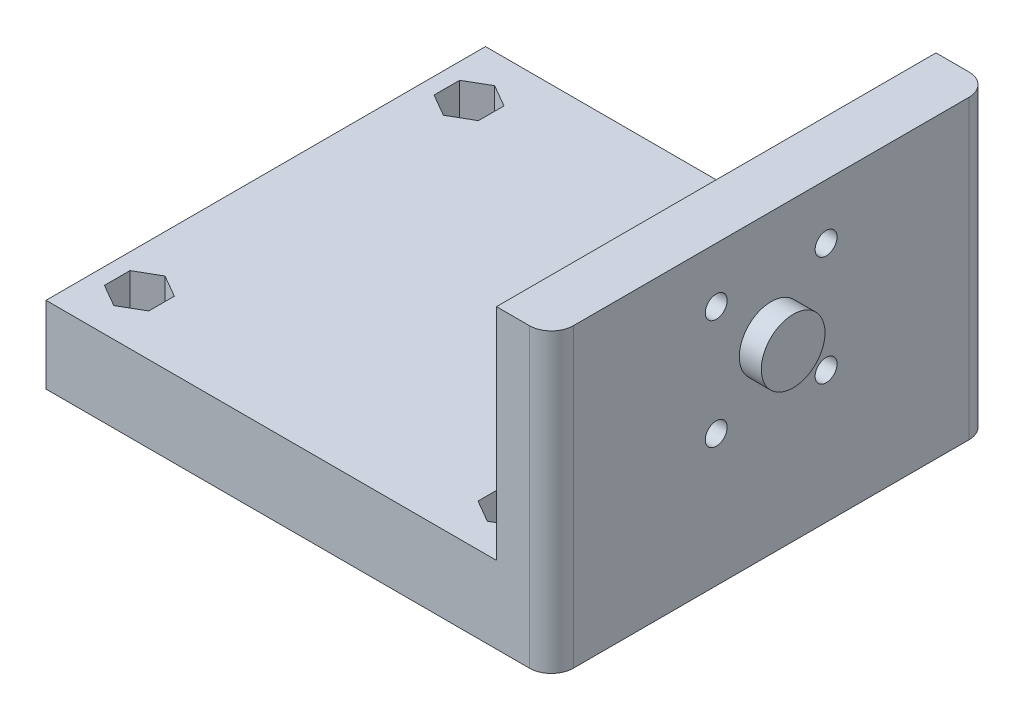
SolidWorks part; units mm, degrees
ref_plane "Plan de face" through (0, 0, 0) normal (0, 0, 1) x (1, 0, 0)
ref_plane "Plan de dessus" through (0, 0, 0) normal (0, 1, 0) x (1, 0, 0)
ref_plane "Plan de droite" through (0, 0, 0) normal (1, 0, 0) x (0, 0, -1)
sketch "Esquisse1" plane through (0, 0, 0) normal (0, 1, 0) x (1, 0, 0)
  line L1 (0, 20) -> (-5, 20)
  line L2 (0, 20) -> (0, -20)
  line L3 (0, -20) -> (-5, -20)
  line L4 (-5, 20) -> (-5, -20)
  dimension "D1" = 5
  dimension "D2" = 40
  dimension "D3" = 20
extrude "Boss.-Extru.1" add sketch "Esquisse1" against normal blind 27
sketch "Esquisse2" plane through (-5, 0, 0) normal (-1, 0, 0) x (0, 0, 1)
  line L0 (-20, -27) -> (-20, 0) construction
  line L1 (20, -27) -> (-20, -27)
  line L2 (20, -27) -> (20, -20)
  line L3 (20, -20) -> (-20, -20)
  line L4 (-20, -27) -> (-20, -20)
  dimension "D1" = 7
extrude "Boss.-Extru.2" add sketch "Esquisse2" along normal blind 41
fillet "Congé1" radius 2 2 edges at (0, -13.5, -20) (0, -13.5, 20)
sketch "Esquisse4" plane through (0, 0, 0) normal (1, 0, 0) x (0, 0, -1)
  circle A0 centre (-5, -5) radius 1
  circle A1 centre (5, -5) radius 1
  circle A2 centre (-5, -15) radius 1
  circle A3 centre (5, -15) radius 1
  dimension "D1" = 10
  dimension "D3" = 2
  dimension "D2" = 10
  dimension "D4" = 5
  dimension "D5" = 5
extrude "Enlèv. mat.-Extru.1" cut sketch "Esquisse4" against normal up to next
sketch "Esquisse5" plane through (0, 0, 0) normal (1, 0, 0) x (0, 0, -1)
  line L1 (-18, 0) -> (18, 0) construction
  line L4 (20, 0) -> (20, -27) construction
  circle A0 centre (0, -10) radius 2.9
  dimension "D1" = 5.8
  dimension "D2" = 10
  dimension "D4" = 20
extrude "Boss.-Extru.3" add sketch "Esquisse5" along normal blind 2
sketch "Esquisse7" plane through (-5, 0, 0) normal (-1, 0, 0) x (0, 0, 1)
  line L1 (-3.835, -7.0178) -> (-2.67, -5)
  line L2 (-2.67, -5) -> (-3.835, -2.9822)
  line L3 (-3.835, -2.9822) -> (-6.165, -2.9822)
  line L4 (-6.165, -2.9822) -> (-7.33, -5)
  line L5 (-7.33, -5) -> (-6.165, -7.0178)
  line L6 (-6.165, -7.0178) -> (-3.835, -7.0178)
  line L7 (3.835, -2.9822) -> (2.67, -5)
  line L8 (2.67, -5) -> (3.835, -7.0178)
  line L9 (3.835, -7.0178) -> (6.165, -7.0178)
  line L10 (6.165, -7.0178) -> (7.33, -5)
  line L11 (7.33, -5) -> (6.165, -2.9822)
  line L12 (6.165, -2.9822) -> (3.835, -2.9822)
  line L13 (-3.835, -17.0178) -> (-2.67, -15)
  line L14 (-2.67, -15) -> (-3.835, -12.9822)
  line L15 (-3.835, -12.9822) -> (-6.165, -12.9822)
  line L16 (-6.165, -12.9822) -> (-7.33, -15)
  line L17 (-7.33, -15) -> (-6.165, -17.0178)
  line L18 (-6.165, -17.0178) -> (-3.835, -17.0178)
  line L19 (7.33, -15) -> (6.165, -12.9822)
  line L20 (6.165, -12.9822) -> (3.835, -12.9822)
  line L21 (3.835, -12.9822) -> (2.67, -15)
  line L22 (2.67, -15) -> (3.835, -17.0178)
  line L23 (3.835, -17.0178) -> (6.165, -17.0178)
  line L24 (6.165, -17.0178) -> (7.33, -15)
  line L25 (18, 0) -> (-18, 0) construction
  line L26 (-20, 0) -> (20, 0) construction
  circle A0 centre (-5, -5) radius 2.0178 construction
  circle A1 centre (5, -5) radius 2.0178 construction
  circle A2 centre (-5, -15) radius 2.0178 construction
  circle A3 centre (5, -15) radius 2.0178 construction
  circle A4 centre (5, -15) radius 1 construction
  dimension "D1" = 2.33
  dimension "D2" = 2.33
  dimension "D3" = 2.33
  dimension "D4" = 2.33
extrude "Enlèv. mat.-Extru.3" cut sketch "Esquisse7" against normal blind 3
sketch "Esquisse9" plane through (0, -20, 0) normal (0, 1, 0) x (1, 0, 0)
  line L0 (-5, -20) -> (-5, 20) construction
  line L1 (-46, -20) -> (-46, 20) construction
  line L4 (-46, -20) -> (-46, 20) construction
  circle A0 centre (-8.5, 15) radius 1
  circle A1 centre (-8.5, -15) radius 1
  circle A2 centre (-42.5, -15) radius 1
  circle A3 centre (-42.5, 15) radius 1
  point P8 (-46, 0)
  dimension "D1" = 2
  dimension "D5" = 15
  dimension "D2" = 3.5
  dimension "D3" = 3.5
  dimension "D4" = 30
extrude "Enlèv. mat.-Extru.5" cut sketch "Esquisse9" against normal through all
sketch "Esquisse8" plane through (0, -20, 0) normal (0, 1, 0) x (1, 0, 0)
  line L0 (-5, -20) -> (-5, 20) construction
  line L1 (-10.5178, 13.835) -> (-8.5, 12.67)
  line L2 (-8.5, 12.67) -> (-6.4822, 13.835)
  line L3 (-6.4822, 13.835) -> (-6.4822, 16.165)
  line L4 (-6.4822, 16.165) -> (-8.5, 17.33)
  line L5 (-8.5, 17.33) -> (-10.5178, 16.165)
  line L6 (-10.5178, 16.165) -> (-10.5178, 13.835)
  line L7 (-10.5178, -16.165) -> (-8.5, -17.33)
  line L8 (-8.5, -17.33) -> (-6.4822, -16.165)
  line L9 (-6.4822, -16.165) -> (-6.4822, -13.835)
  line L10 (-6.4822, -13.835) -> (-8.5, -12.67)
  line L11 (-8.5, -12.67) -> (-10.5178, -13.835)
  line L12 (-10.5178, -13.835) -> (-10.5178, -16.165)
  line L13 (-44.5178, -16.165) -> (-42.5, -17.33)
  line L14 (-42.5, -17.33) -> (-40.4822, -16.165)
  line L15 (-40.4822, -16.165) -> (-40.4822, -13.835)
  line L16 (-40.4822, -13.835) -> (-42.5, -12.67)
  line L17 (-42.5, -12.67) -> (-44.5178, -13.835)
  line L18 (-44.5178, -13.835) -> (-44.5178, -16.165)
  line L19 (-42.5, 12.67) -> (-40.4822, 13.835)
  line L20 (-40.4822, 13.835) -> (-40.4822, 16.165)
  line L21 (-40.4822, 16.165) -> (-42.5, 17.33)
  line L22 (-42.5, 17.33) -> (-44.5178, 16.165)
  line L23 (-44.5178, 16.165) -> (-44.5178, 13.835)
  line L24 (-44.5178, 13.835) -> (-42.5, 12.67)
  circle A0 centre (-8.5, 15) radius 2.0178 construction
  circle A1 centre (-8.5, -15) radius 2.0178 construction
  circle A2 centre (-42.5, -15) radius 2.0178 construction
  circle A3 centre (-42.5, 15) radius 2.0178 construction
  circle A4 centre (-8.5, 15) radius 1 construction
  circle A5 centre (-8.5, -15) radius 1 construction
  circle A7 centre (-42.5, 15) radius 1 construction
  dimension "D1" = 2.33
  dimension "D2" = 2.33
  dimension "D3" = 2.33
  dimension "D4" = 2.33
extrude "Enlèv. mat.-Extru.4" cut sketch "Esquisse8" against normal blind 4
